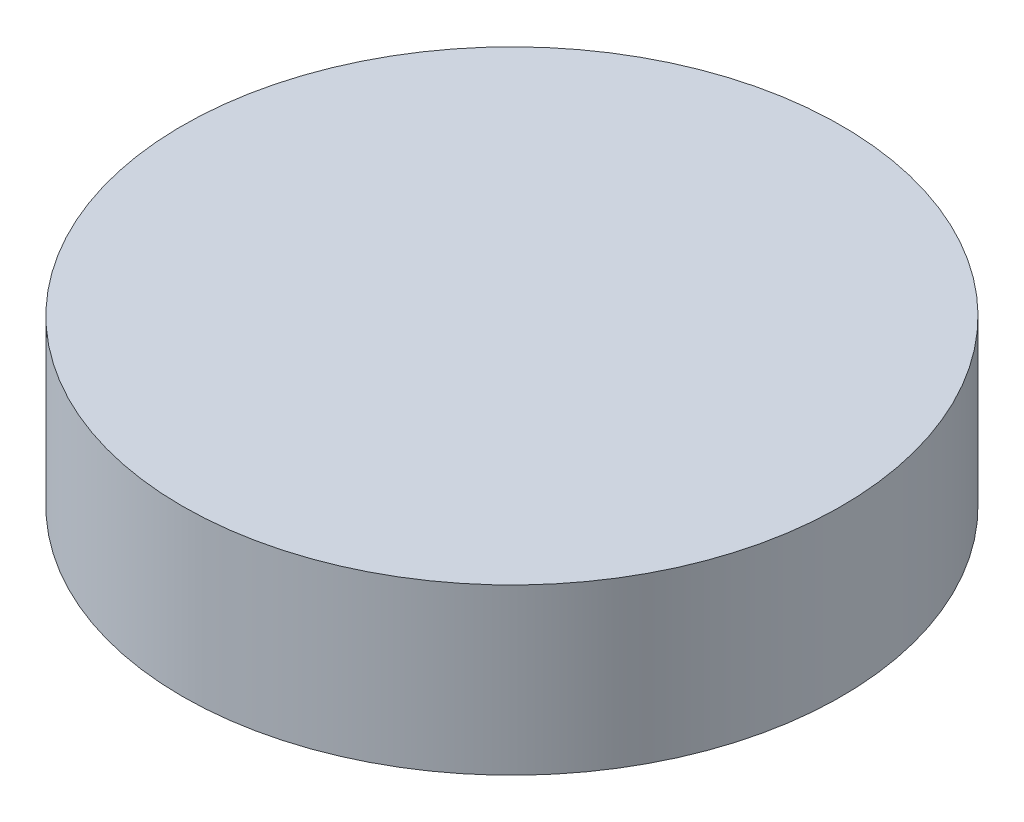
SolidWorks part; units mm, degrees
ref_plane "Front Plane" through (0, 0, 0) normal (0, 0, 1) x (1, 0, 0)
ref_plane "Top Plane" through (0, 0, 0) normal (0, 1, 0) x (1, 0, 0)
ref_plane "Right Plane" through (0, 0, 0) normal (1, 0, 0) x (0, 0, -1)
sketch "Sketch1" plane through (0, 0, 0) normal (0, 1, 0) x (1, 0, 0)
  circle A0 centre (0, 0) radius 3
  dimension "D1" = 6
extrude "Boss-Extrude1" add sketch "Sketch1" along normal blind 1.5
